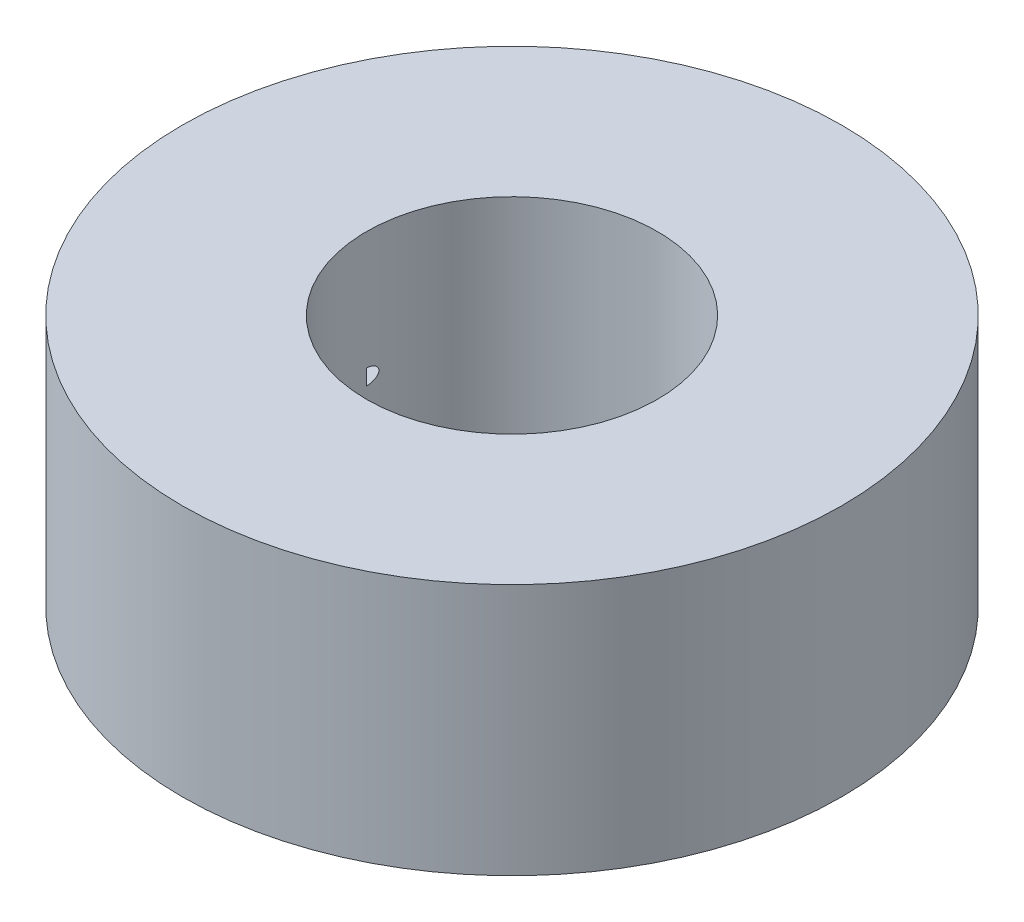
SolidWorks part; units mm, degrees
ref_plane "Front Plane" through (0, 0, 0) normal (0, 0, 1) x (1, 0, 0)
ref_plane "Top Plane" through (0, 0, 0) normal (0, 1, 0) x (1, 0, 0)
ref_plane "Right Plane" through (0, 0, 0) normal (1, 0, 0) x (0, 0, -1)
sketch "Sketch1" plane through (0, 0, 0) normal (0, 1, 0) x (1, 0, 0)
  circle A0 centre (0, 0) radius 7.5
  circle A1 centre (0, 0) radius 17
  dimension "D1" = 15
  dimension "D2" = 34
extrude "Boss-Extrude1" add sketch "Sketch1" along normal blind 13
sketch "Sketch2" plane through (0, 0, 0) normal (0, 0, 1) x (1, 0, 0)
  line L0 (-10.65, 13) -> (-10.65, 0) construction
  line L1 (17, 13) -> (-17, 13) construction
  line L2 (-17, 0) -> (17, 0) construction
  line L3 (-17, 13) -> (-17, 0) construction
  circle A0 centre (-10.65, 6.5) radius 3.175
  point P8 (-8.3314, 5.5248)
  point P9 (-10.65, 6.5)
  point P10 (-11.2827, 6.5)
  dimension "D1" = 6.35
  dimension "D2" = 6.35
extrude "Cut-Extrude1" cut sketch "Sketch2" against normal through all
